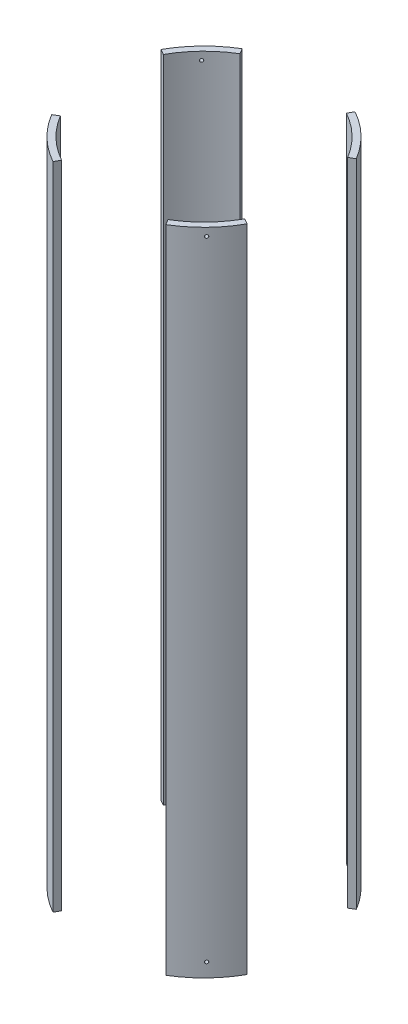
SolidWorks part; units mm, degrees
material "6061-T6 (SS)"
ref_plane "Front Plane" through (0, 0, 0) normal (0, 0, 1) x (1, 0, 0)
ref_plane "Top Plane" through (0, 0, 0) normal (0, 1, 0) x (1, 0, 0)
ref_plane "Right Plane" through (0, 0, 0) normal (1, 0, 0) x (0, 0, -1)
sketch "Sketch2" plane through (0, 0, 0) normal (0, 1, 0) x (1, 0, 0)
  circle A0 centre (0, 0) radius 88.9
  circle A1 centre (0, 0) radius 83.82
  dimension "D1" = 177.8
  dimension "D2" = 167.64
extrude "Boss-Extrude1" add sketch "Sketch2" along normal mid plane 520.4155
sketch "Sketch3" plane through (0, 0, 0) normal (0, 1, 0) x (1, 0, 0)
  line L0 (0, 0) -> (169.6618, 101.6776)
  line L1 (-58.1167, 96.9749) -> (0, 0)
  line L2 (0, 0) -> (53.9, 96.9749)
  line L3 (53.9, 96.9749) -> (-58.1167, 96.9749)
  line L4 (0, 0) -> (70.9917, -118.4586)
  line L5 (70.9917, -118.4586) -> (-65.8409, -118.4586)
  line L6 (-65.8409, -118.4586) -> (0, 0)
  line L7 (169.6618, 101.6776) -> (169.6618, -94.3004)
  line L8 (169.6618, -94.3004) -> (0, 0)
  line L9 (0, 0) -> (-123.7413, 68.7771)
  line L10 (-123.7413, 68.7771) -> (-123.7413, -74.1577)
  line L11 (-123.7413, -74.1577) -> (0, 0)
  dimension "D1" = 60
  dimension "D2" = 60
  dimension "D3" = 60
  dimension "D4" = 60
  dimension "D5" = 30
  dimension "D6" = 30
extrude "Cut-Extrude1" cut sketch "Sketch3" against normal through all both and the other way through all contours L8 L7 L0 | L2 L3 L1 | L10 L11 L9 | L6 L5 L4
ref_plane "Bolt reference plane" through (-56.3092, 0, 58.1758) normal (0.6955, 0, -0.7185) x (-0.7185, 0, -0.6955)
sketch "Sketch5" plane through (-56.3092, 0, 58.1758) normal (0.6955, 0, -0.7185) x (-0.7185, 0, -0.6955)
  line L0 (-23.009, -260.2078) -> (23.009, -260.2078) construction
  circle A0 centre (-0.0228, 253.8578) radius 1.27
  circle A1 centre (-0.0228, -249.0953) radius 1.27
  dimension "D1" = 2.54
  dimension "D4" = 11.1125
  dimension "D2" = 21.717
  dimension "D3" = 6.35
extrude "Bolt holes" cut sketch "Sketch5" against normal through all
pattern_circular "Bolt pattern" count 4 over 360 about axis through (0, 260.2078, 0) along (0, 1, 0) of "Bolt holes"
equation "\"D1@Boss-Extrude1\"=3*12"
